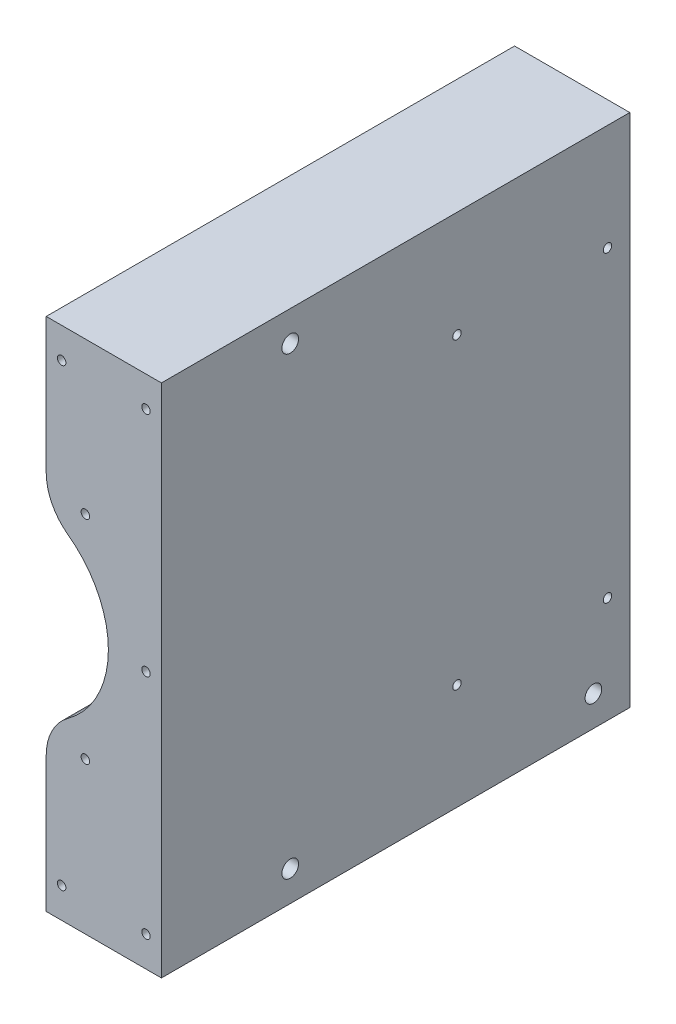
SolidWorks part; units mm, degrees
ref_plane "Front Plane" through (0, 0, 0) normal (0, 0, 1) x (1, 0, 0)
ref_plane "Top Plane" through (0, 0, 0) normal (0, 1, 0) x (1, 0, 0)
ref_plane "Right Plane" through (0, 0, 0) normal (1, 0, 0) x (0, 0, -1)
sketch "Sketch1" plane through (0, 0, 0) normal (0, 0, 1) x (1, 0, 0)
  line L0 (-19, -40.3698) -> (-19, -85)
  line L1 (-19, -85) -> (19, -85)
  line L2 (19, -85) -> (19, 85)
  line L3 (19, 85) -> (-19, 85)
  line L4 (-19, 85) -> (-19, 40.3704)
  circle A0 centre (-6.0838, -35) radius 1.4
  circle A1 centre (13.9162, -75) radius 1.4
  circle A2 centre (-13.9162, -75) radius 1.4
  circle A3 centre (13.9162, 75) radius 1.4
  circle A4 centre (13.9162, 0) radius 1.4
  circle A5 centre (-6.0838, 35) radius 1.4
  circle A6 centre (-13.9162, 75) radius 1.4
  arc A7 (-11.825, -26.2403) -> (-19, -40.3698) centre (-1.5, -40.3698) ccw
  arc A8 (-19, 40.3704) -> (-11.825, 26.2409) centre (-1.5, 40.3704) ccw
  arc A9 (-11.825, -26.2403) -> (-11.825, 26.2409) centre (-31.0001, 0.0003) ccw
extrude "Boss-Extrude1" add sketch "Sketch1" along normal blind 154.5
sketch "Sketch2" plane through (19, 0, 0) normal (1, 0, 0) x (0, 0, -1)
  circle A0 centre (-7.3487, 50) radius 1.4
  circle A1 centre (-56.9997, 50) radius 1.4
  circle A2 centre (-7.3487, -50) radius 1.4
  circle A3 centre (-56.9997, -50) radius 1.4
  circle A4 centre (-11.9997, -75) radius 2.75
  circle A5 centre (-111.9997, -75) radius 2.75
  circle A6 centre (-111.9997, 75) radius 2.75
extrude "Cut-Extrude2" cut sketch "Sketch2" against normal blind 154.5
